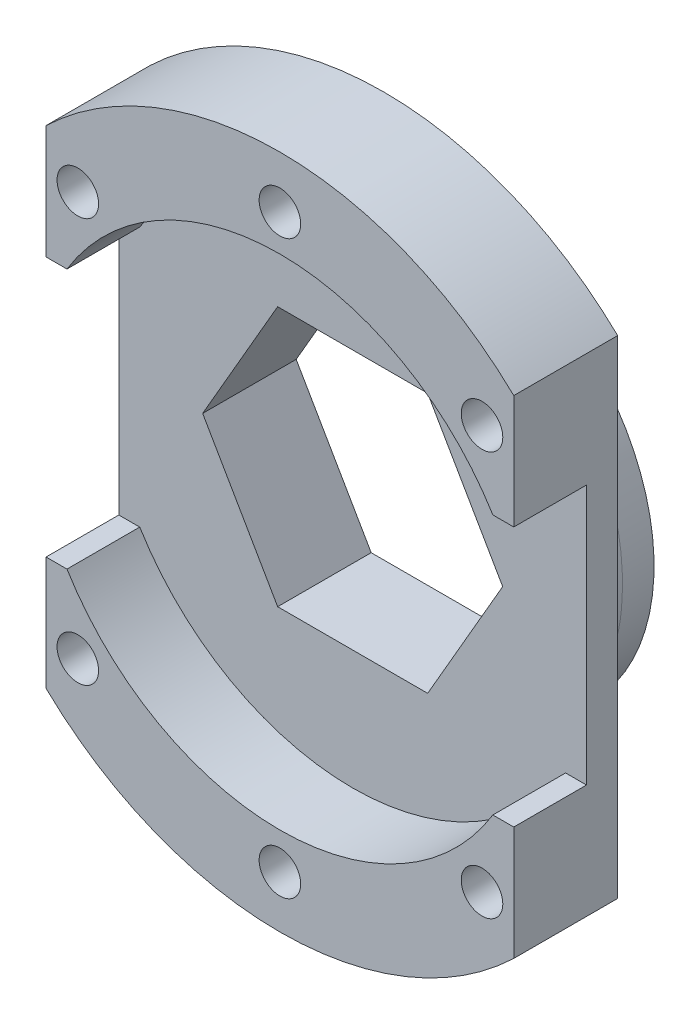
SolidWorks part; units mm, degrees
ref_plane "Front Plane" through (0, 0, 0) normal (0, 0, 1) x (1, 0, 0)
ref_plane "Top Plane" through (0, 0, 0) normal (0, 1, 0) x (1, 0, 0)
ref_plane "Right Plane" through (0, 0, 0) normal (1, 0, 0) x (0, 0, -1)
sketch "Sketch1" plane through (0, 0, 0) normal (0, 0, 1) x (1, 0, 0)
  circle A0 centre (0, 0) radius 32.5
  dimension "D1" = 65
extrude "Boss-Extrude1" add sketch "Sketch1" along normal blind 10
sketch "Sketch2" plane through (0, 0, 10) normal (0, 0, 1) x (1, 0, 0)
  line L1 (14.4338, 0) -> (7.2169, 12.5)
  line L2 (7.2169, 12.5) -> (-7.2169, 12.5)
  line L3 (-7.2169, 12.5) -> (-14.4338, 0)
  line L4 (-14.4338, 0) -> (-7.2169, -12.5)
  line L5 (-7.2169, -12.5) -> (7.2169, -12.5)
  line L6 (7.2169, -12.5) -> (14.4338, 0)
  circle A0 centre (0, 0) radius 12.5 construction
  dimension "D1" = 25
extrude "Cut-Extrude1" cut sketch "Sketch2" against normal blind 5
sketch "Sketch3" plane through (0, 0, 10) normal (0, 0, 1) x (1, 0, 0)
  circle A0 centre (0, 27.5) radius 2
  circle A1 centre (19.4454, 19.4454) radius 2
  circle A2 centre (27.5, 0) radius 2
  circle A3 centre (19.4454, -19.4454) radius 2
  circle A4 centre (0, -27.5) radius 2
  circle A5 centre (-19.4454, -19.4454) radius 2
  circle A6 centre (-27.5, 0) radius 2
  circle A7 centre (-19.4454, 19.4454) radius 2
  point P20 (0, 0)
  dimension "D1" = 4
  dimension "D2" = 27.5
  dimension "D3" = 8
extrude "Cut-Extrude2" cut sketch "Sketch3" against normal through all
sketch "Sketch4" plane through (0, 0, 0) normal (0, 0, -1) x (-1, 0, 0)
  line L1 (14.4338, 0) -> (7.2169, 12.5)
  line L2 (7.2169, 12.5) -> (-7.2169, 12.5)
  line L3 (-7.2169, 12.5) -> (-14.4338, 0)
  line L4 (-14.4338, 0) -> (-7.2169, -12.5)
  line L5 (-7.2169, -12.5) -> (7.2169, -12.5)
  line L6 (7.2169, -12.5) -> (14.4338, 0)
  circle A0 centre (0, 0) radius 20
  circle A1 centre (0, 0) radius 12.5 construction
  dimension "D1" = 40
extrude "Boss-Extrude2" add sketch "Sketch4" along normal blind 6
sketch "Sketch5" plane through (0, 0, 10) normal (0, 0, 1) x (1, 0, 0)
  line L2 (22.5, 23.4521) -> (22.5, -23.4521)
  line L4 (-22.5, 23.4521) -> (-22.5, -23.4521)
  line L5 (22.5, 23.4521) -> (-22.5, -23.4521) construction
  line L6 (22.5, -23.4521) -> (-22.5, 23.4521) construction
  circle A0 centre (0, 0) radius 32.5 construction
  arc A1 (-22.5, 23.4521) -> (-22.5, -23.4521) centre (0, 0) ccw
  arc A2 (22.5, -23.4521) -> (22.5, 23.4521) centre (0, 0) ccw
  point P0 (0, 0)
  dimension "D1" = 45
extrude "Cut-Extrude3" cut sketch "Sketch5" against normal through all
sketch "Sketch6" plane through (0, 0, 10) normal (0, 0, 1) x (1, 0, 0)
  circle A0 centre (0, 0) radius 24
  dimension "D1" = 48
extrude "Cut-Extrude5" cut sketch "Sketch6" against normal blind 7
sketch "Sketch7" plane through (0, 0, 0) normal (0, 0, -1) x (-1, 0, 0)
  line L1 (14.4338, 0) -> (7.2169, 12.5)
  line L2 (7.2169, 12.5) -> (-7.2169, 12.5)
  line L3 (-7.2169, 12.5) -> (-14.4338, 0)
  line L4 (-14.4338, 0) -> (-7.2169, -12.5)
  line L5 (-7.2169, -12.5) -> (7.2169, -12.5)
  line L6 (7.2169, -12.5) -> (14.4338, 0)
  circle A0 centre (0, 0) radius 12.5 construction
extrude "Cut-Extrude6" cut sketch "Sketch7" against normal through all
sketch "Sketch8" plane through (0, 0, 3) normal (0, 0, 1) x (1, 0, 0)
  line L0 (-22.5, 8.3516) -> (-22.5, 23.4521) construction
  line L1 (22.5, -12.5) -> (-22.5, -12.5)
  line L2 (22.5, -12.5) -> (22.5, 12.5)
  line L3 (22.5, 12.5) -> (-22.5, 12.5)
  line L4 (-22.5, -12.5) -> (-22.5, 12.5)
  line L5 (22.5, -12.5) -> (-22.5, 12.5) construction
  line L6 (22.5, 12.5) -> (-22.5, -12.5) construction
  point P0 (0, 0)
  dimension "D1" = 25
extrude "Cut-Extrude7" cut sketch "Sketch8" along normal through all
fillet "Fillet1" radius 3 1 edges at (20, 0, 0)
